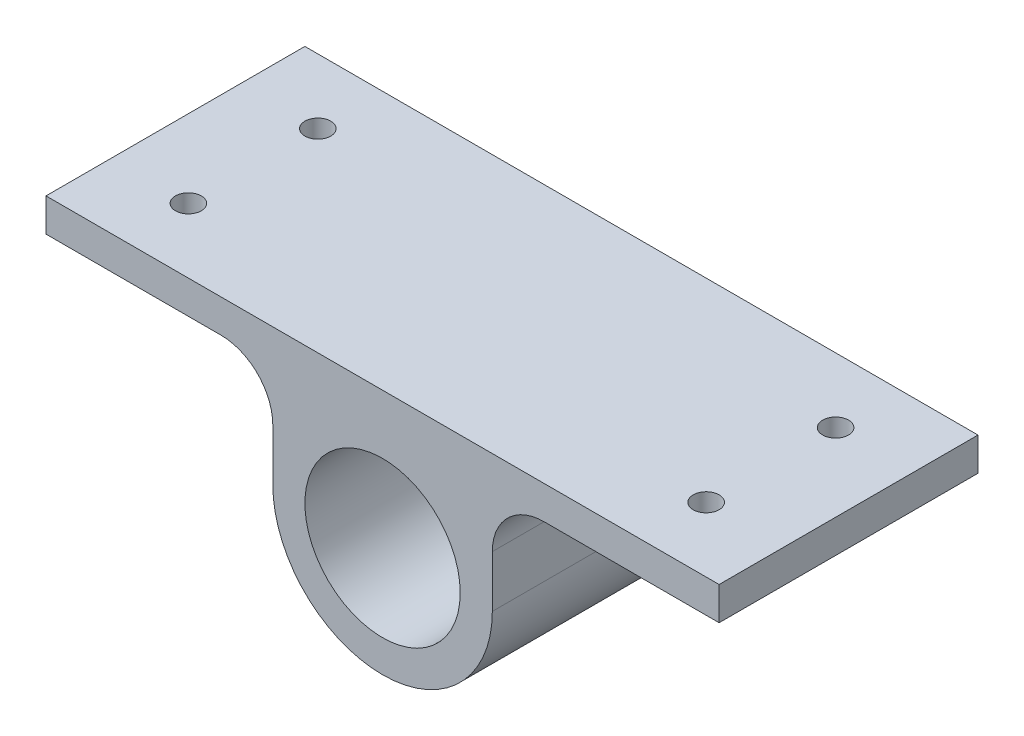
SolidWorks part; units mm, degrees
ref_plane "Front Plane" through (0, 0, 0) normal (0, 0, 1) x (1, 0, 0)
ref_plane "Top Plane" through (0, 0, 0) normal (0, 1, 0) x (1, 0, 0)
ref_plane "Right Plane" through (0, 0, 0) normal (1, 0, 0) x (0, 0, -1)
sketch "Sketch1" plane through (0, 0, 0) normal (0, 0, 1) x (1, 0, 0)
  line L0 (-325, 132) -> (325, 132)
  line L1 (325, 132) -> (325, 100)
  line L2 (325, 100) -> (156, 100)
  line L3 (106, 50) -> (106, 0)
  line L4 (-106, 0) -> (-106, 50)
  line L5 (-156, 100) -> (-325, 100)
  line L6 (-325, 100) -> (-325, 132)
  line L7 (0, -133.1836) -> (0, 151.3854) construction
  arc A1 (106, 0) -> (-106, 0) centre (0, 0) cw
  arc A2 (-106, 50) -> (-156, 100) centre (-156, 50) ccw
  arc A3 (106, 50) -> (156, 100) centre (156, 50) cw
  dimension "D2" = 132
  dimension "D5" = 106
  dimension "D6" = 50
  dimension "D1" = 32
  dimension "D4" = 325
extrude "Boss-Extrude1" add sketch "Sketch1" along normal blind 250
sketch "Sketch2" plane through (0, 0, 250) normal (0, 0, 1) x (1, 0, 0)
  circle A0 centre (0, 0) radius 75
  dimension "D1" = 150
extrude "Cut-Extrude1" cut sketch "Sketch2" against normal blind 250
sketch "Sketch3" plane through (0, 132, 0) normal (0, 1, 0) x (1, 0, 0)
  line L0 (0, 114.4406) -> (0, -300.1433) construction
  line L1 (-250, 58.1804) -> (-250, -310.8595) construction
  line L2 (-400.5188, -62.5) -> (-106.4925, -62.5) construction
  line L3 (-400.5188, -187.5) -> (-106.4925, -187.5) construction
  line L4 (325, 0) -> (-325, 0) construction
  line L5 (-325, -250) -> (-325, 0) construction
  circle A0 centre (-250, -62.5) radius 12.5
  circle A1 centre (-250, -187.5) radius 12.5
  circle A2 centre (250, -187.5) radius 12.5
  circle A3 centre (250, -62.5) radius 12.5
  dimension "D4" = 25
  dimension "D1" = 62.5
  dimension "D2" = 125
  dimension "D3" = 75
extrude "Cut-Extrude2" cut sketch "Sketch3" against normal blind 250
